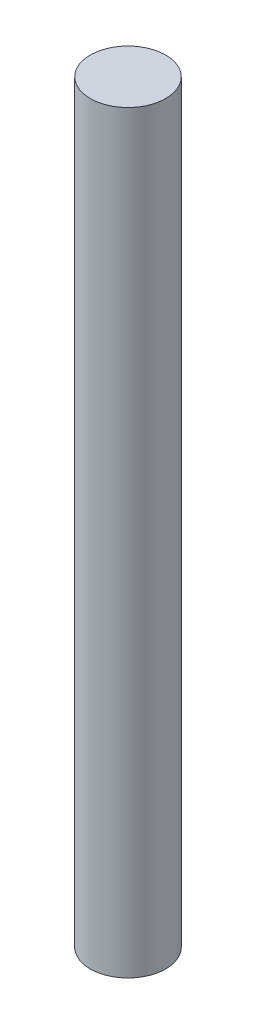
SolidWorks part; units mm, degrees
ref_plane "Alzado" through (0, 0, 0) normal (0, 0, 1) x (1, 0, 0)
ref_plane "Planta" through (0, 0, 0) normal (0, 1, 0) x (1, 0, 0)
ref_plane "Vista lateral" through (0, 0, 0) normal (1, 0, 0) x (0, 0, -1)
sketch "Sketch1" plane through (0, 0, 0) normal (0, 1, 0) x (1, 0, 0)
  circle A0 centre (0, 0) radius 7.5
  dimension "D1" = 15
extrude "Boss-Extrude1" add sketch "Sketch1" along normal mid plane 150
